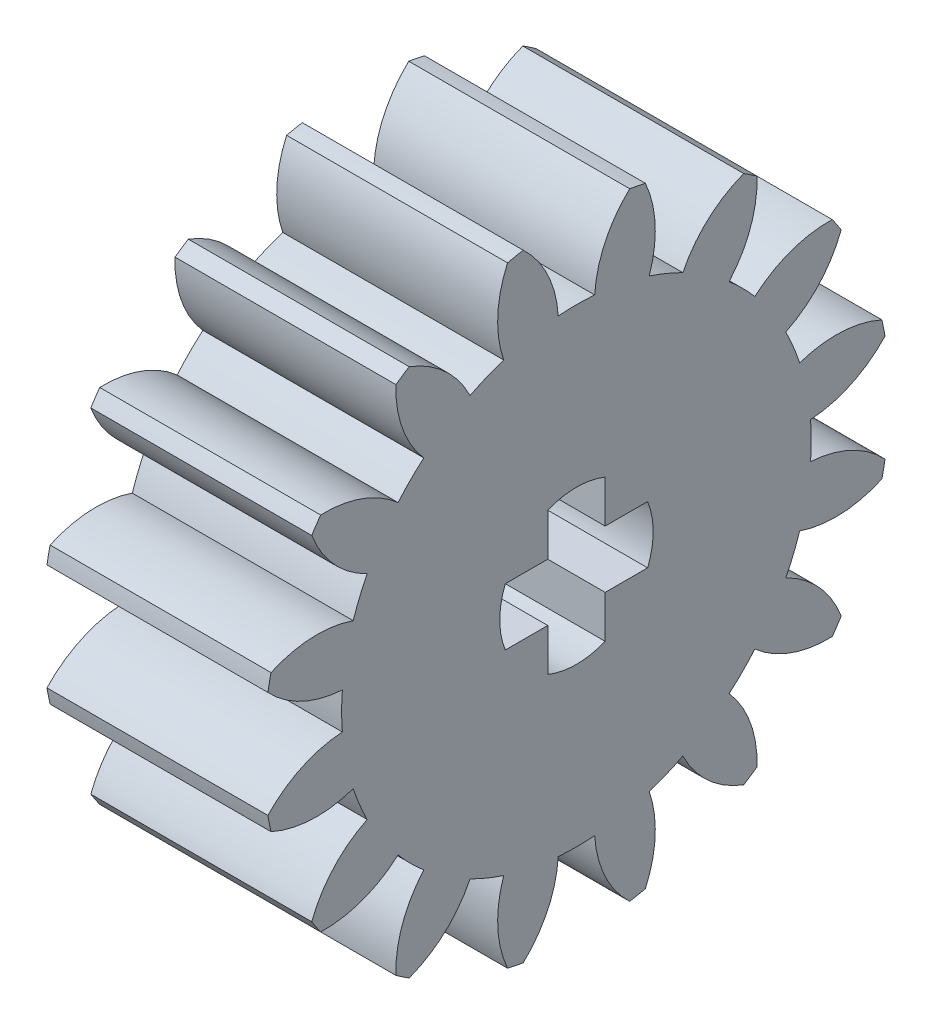
SolidWorks part; units mm, degrees
ref_plane "Plane1" through (0, 0, 0) normal (0, 0, 1) x (1, 0, 0)
ref_plane "Plane2" through (0, 0, 0) normal (0, 1, 0) x (1, 0, 0)
ref_plane "Plane3" through (0, 0, 0) normal (1, 0, 0) x (0, 0, -1)
sketch "HoldingSke" plane through (0, 0, 0) normal (0, 1, 0) x (1, 0, 0)
  line L0 (0, 0) -> (0.9613, -0.2756)
  line L1 (-15, 0) -> (100, 0) construction
  line L2 (0, 0) -> (-2.1039, 2.3779)
  line L3 (0, 0) -> (-11.863, 4.5341)
  line L4 (0, 0) -> (8.3015, 2.3804)
  line L5 (0, 0) -> (-46.8476, -17.4728)
  line L6 (0, 0) -> (-5.2639, -3.5516)
  line L7 (-2.1039, 2.3779) -> (8.6588, 51.2067)
  line L8 (-76.2, 54.61) -> (-76.1, 54.61)
  line L9 (-71.009, 38.7566) -> (-53.1078, 45.2721)
  line L10 (-76.2, 71.12) -> (104.1128, 71.12)
  line L11 (0, 0) -> (-6.35, 0)
  line L12 (-76.2, 101.6) -> (-76.162, 101.6)
  line L13 (24.9733, 27.94) -> (52.9518, 28.4284)
  line L14 (24.9733, 27.94) -> (24.9743, 27.94)
  line L15 (24.9733, 27.94) -> (100.4006, 29.5858)
  line L16 (-63.627, -1) -> (-12.827, -1)
  circle A0 centre (0, 0) radius 0.5
  circle A1 centre (0, 0) radius 6.749
  circle A2 centre (0, 0) radius 37.5
  circle A3 centre (0, 0) radius 0.5
  dimension "MHD" = 13.498
  dimension "Hub_dia" = 75
  dimension "Bore" = 1
  dimension "MBD" = 1
  dimension "Num_teeth" = 16
  dimension "Pitch_radius" = 180.3128
  dimension "Pitch" = 1
  dimension "Width" = 6.35
  dimension "Overall_len" = 50
  dimension "Show_teeth" = 16
  dimension "Thickness" = 6.35
  dimension "OAL" = 50.0009
  dimension "T_dim" = 0.1
  dimension "Ap" = 20
  dimension "H" = 19.05
  dimension "Backlash" = 0.038
  dimension "Addendum_fac" = 1
  dimension "Dedendum_fac" = 1.25
  dimension "Clearance_fac" = 0.25
  dimension "Dedendum_add" = 0.001
  dimension "Module" = 1
sketch "BasProSke" plane through (0, 0, 0) normal (0, 1, 0) x (1, 0, 0)
  line L0 (-10, 0) -> (60, 0) construction
  line L1 (0, 0) -> (0, 9)
  line L2 (0, 0) -> (6.35, 0)
  line L3 (6.35, 0) -> (6.35, 9)
  line L4 (6.35, 9) -> (0, 9)
  dimension "Diameter" = 18
  dimension "Thickness" = 6.35
revolve "Base-Revolve" add sketch "BasProSke" angle 360 about L0
sketch "TooCutSke" plane through (0, 0, 0) normal (1, 0, 0) x (0, 0, -1)
  line L1 (0, 0) -> (0, 107) construction
  line L2 (0, 0) -> (-0.8506, 7.9547) construction
  line L3 (0, 0) -> (-3.1089, 15.6293) construction
  line L4 (-0.8506, 7.9547) -> (-1.5544, 7.8146) construction
  arc A0 (0.5238, 6.7286) -> (-0.5238, 6.7286) centre (0, 0) ccw
  arc A1 (1.5534, 8.8907) -> (-1.5534, 8.8907) centre (0, 0) ccw
  circle A2 centre (0, 0) radius 8 construction
  circle A3 centre (0, 0) radius 7.5175 construction
  arc A4 (-0.5238, 6.7286) -> (-1.5534, 8.8907) centre (-3.7179, 6.5338) ccw
  arc A5 (1.5534, 8.8907) -> (0.5238, 6.7286) centre (3.7179, 6.5338) ccw
  dimension "Root_dia" = 13.498
  dimension "Overcut_dia" = 18.0508
  dimension "Pitch_dia" = 16
  dimension "Base_dia" = 15.0351
  dimension "Flank_rad" = 3.2
  dimension "Half_ang" = 11.25
  dimension "Half_CT" = 0.7176
extrude "ToothCut" cut sketch "TooCutSke" along normal through all
fillet "Breaks" [suppressed] radius 0.02
fillet "RootFillets" [suppressed] radius 0.251
pattern_circular "TeethCuts" count 16 every 22.5 about axis through (-10, 0, 0) along (1, 0, 0) of "ToothCut", "RootFillets", "Breaks"
sketch "HubNeaOneSke" plane through (0, 0, 0) normal (-1, 0, 0) x (0, 0, 1)
  circle A0 centre (0, 0) radius 6.749
  dimension "Diameter" = 13.498
extrude "HubNearOne" [suppressed] add sketch "HubNeaOneSke" along normal blind 43.6509
sketch "HubNeaBotSke" plane through (0, 0, 0) normal (-1, 0, 0) x (0, 0, 1)
  circle A0 centre (0, 0) radius 6.749
  dimension "Diameter" = 13.498
extrude "HubNearBoth" [suppressed] add sketch "HubNeaBotSke" along normal blind 21.8254
ref_plane "FarPln" through (6.35, 0, 0) normal (1, 0, 0) x (0, 0, -1)
sketch "HubFarSke" plane through (6.35, 0, 0) normal (1, 0, 0) x (0, 0, -1)
  circle A0 centre (0, 0) radius 6.749
  dimension "Diameter" = 13.498
extrude "HubFar" [suppressed] add sketch "HubFarSke" along normal blind 21.8254
sketch "BorSke" plane through (0, 0, 0) normal (1, 0, 0) x (0, 0, -1)
  circle A0 centre (0, 0) radius 0.5
  dimension "Diameter" = 1
extrude "Bore" cut sketch "BorSke" along normal mid plane 100.0017
sketch "KeySke" plane through (0, 0, 0) normal (1, 0, 0) x (0, 0, -1)
  line L0 (-0.05, 0) -> (-0.05, 0.6)
  line L1 (-0.05, 0.6) -> (0.05, 0.6)
  line L2 (0.05, 0.6) -> (0.05, 0)
  line L3 (0, 0) -> (0, 34) construction
  line L4 (-0.05, 0) -> (0.05, 0)
  dimension "Offset" = 0.6
  dimension "Width" = 0.1
extrude "Keyway" [suppressed] cut sketch "KeySke" along normal mid plane 100.0017
pattern_circular "Keyway2" [suppressed] count 2 every 90 about axis through (-10, 0, 0) along (1, 0, 0)
sketch "Sketch1" plane through (6.35, 0, 0) normal (1, 0, 0) x (0, 0, -1)
  line L0 (-0.8249, 2.0449) -> (-0.8249, 0.8249)
  line L1 (-0.8249, 0.8249) -> (-2.0449, 0.8249)
  line L2 (-2.0449, -0.8249) -> (-0.8249, -0.8249)
  line L3 (-0.8249, -0.8249) -> (-0.8249, -2.0449)
  line L4 (0.8249, -2.0449) -> (0.8249, -0.8249)
  line L5 (0.8249, -0.8249) -> (2.0449, -0.8249)
  line L6 (2.0449, 0.8249) -> (0.8249, 0.8249)
  line L7 (0.8249, 0.8249) -> (0.8249, 2.0449)
  circle A0 centre (0, 0) radius 2.205
  dimension "D1" = 4.41
  dimension "D2" = 1.22
extrude "Cut-Extrude1" cut sketch "Sketch1" against normal blind 10 contours L7 A0 L0 L1 L2 L3 L4 L5 L6
equation "' \"Module@HoldingSke\" = 6.35"
equation "' \"Num_teeth@HoldingSke\" = 12"
equation "' \"Ap@HoldingSke\" =  20"
equation "' \"Width@HoldingSke\" = 0.5 * 25.4"
equation "' \"Hub_dia@HoldingSke\"= 1 * 25.4"
equation "' \"Overall_len@HoldingSke\" = 1.0 * 25.4"
equation "' \"Bore@HoldingSke\" = 0.75 * 25.4"
equation "' \"T_dim@HoldingSke\" = 0.1 * 25.4"
equation "' \"Width@KeySke\" = 0.25 * 25.4"
equation "' \"Show_teeth@HoldingSke\" = 13"
equation "' \"Backlash@HoldingSke\" = 0.009 * 25.4"
equation "' \"Addendum_fac@HoldingSke\" = 1.0"
equation "' \"Dedendum_fac@HoldingSke\" = 1.25"
equation "' \"Dedendum_add@HoldingSke\" = 0.00005 * 25.4"
equation "' \"Clearance_fac@HoldingSke\" = 0.25"
equation "\"Pitch@HoldingSke\" = 1 / \"Module@HoldingSke\""
equation "\"Overcut_dia@TooCutSke\" = (\"Num_teeth@HoldingSke\" + 2 * \"Addendum_fac@HoldingSke\") / \"Pitch@HoldingSke\" + 0.002 * 25.4"
equation "\"Pitch_dia@TooCutSke\" = \"Num_teeth@HoldingSke\" / \"Pitch@HoldingSke\""
equation "\"Base_dia@TooCutSke\" = \"Num_teeth@HoldingSke\" / \"Pitch@HoldingSke\" * cos((\"Ap@HoldingSke\"  * 3.14159265 / 180))"
equation "\"Root_dia@TooCutSke\" = (\"Num_teeth@HoldingSke\" + 2) / \"Pitch@HoldingSke\" - 2 * (\"Addendum_fac@HoldingSke\" + \"Dedendum_fac@HoldingSke\") / \"Pitch@HoldingSke\" - \"Dedendum_add@HoldingSke\" * 2"
equation "\"Half_ang@TooCutSke\" = 180 / \"Num_teeth@HoldingSke\""
equation "\"Half_CT@TooCutSke\" = \"Num_teeth@HoldingSke\" / \"Pitch@HoldingSke\" * sin((3.14159265 / 2 / \"Num_teeth@HoldingSke\")) / 2 - 7 * \"Backlash@HoldingSke\" / 4"
equation "\"Flank_rad@TooCutSke\" = \"Num_teeth@HoldingSke\" / \"Pitch@HoldingSke\" / 5"
equation "\"Radius@RootFillets\" = \"Clearance_fac@HoldingSke\" / \"Pitch@HoldingSke\" + \"Dedendum_add@HoldingSke\""
equation "\"Break_rad@Breaks\" = 0.02 / \"Pitch@HoldingSke\""
equation "\"Thickness@HoldingSke\" = \"Width@HoldingSke\""
equation "\"OAL@HoldingSke\" = \"Thickness@HoldingSke\""
equation "\"MHD@HoldingSke\" = (\"Num_teeth@HoldingSke\" + 2) / \"Pitch@HoldingSke\" - 2 * (\"Addendum_fac@HoldingSke\" + \"Dedendum_fac@HoldingSke\")  / \"Pitch@HoldingSke\" - \"Dedendum_add@HoldingSke\" * 2"
equation "\"MBD@HoldingSke\" = (\"Num_teeth@HoldingSke\" + 2) / \"Pitch@HoldingSke\" - 2 * (\"Addendum_fac@HoldingSke\" + \"Dedendum_fac@HoldingSke\")  / \"Pitch@HoldingSke\" - \"Dedendum_add@HoldingSke\" * 2 - 0.002 * 25.4"
equation "\"MHD@HoldingSke\" = ((sgn( \"MHD@HoldingSke\" - \"Hub_dia@HoldingSke\" )-1)*( \"MHD@HoldingSke\" - \"Hub_dia@HoldingSke\" ))/-2+ \"Hub_dia@HoldingSke\""
equation "\"MBD@HoldingSke\" = ((sgn( \"MBD@HoldingSke\" - \"Bore@HoldingSke\" )-1)*( \"MBD@HoldingSke\" - \"Bore@HoldingSke\" ))/-2+ \"Bore@HoldingSke\""
equation "\"OAL@HoldingSke\" = ((sgn( \"OAL@HoldingSke\" - \"Overall_len@HoldingSke\" )+1)*( \"OAL@HoldingSke\" - \"Overall_len@HoldingSke\" ))/2 + \"Overall_len@HoldingSke\" + 0.000002 * 25.4"
equation "\"Num_teeth@TeethCuts\" = int( \"Show_teeth@HoldingSke\" ) + 1"
equation "\"Num_teeth@TeethCuts\" = ((sgn( \"Num_teeth@TeethCuts\" - \"Num_teeth@HoldingSke\" )-1)*( \"Num_teeth@TeethCuts\" - \"Num_teeth@HoldingSke\" ))/-2+ \"Num_teeth@HoldingSke\""
equation "\"Num_teeth@TeethCuts\" = ((sgn( \"Num_teeth@TeethCuts\" - 2.0)+1)*( \"Num_teeth@TeethCuts\" - 2.0))/2 +2.0"
equation "\"Angle@TeethCuts\" = 360.0 / \"Num_teeth@HoldingSke\""
equation "\"Diameter@BasProSke\" = (\"Num_teeth@HoldingSke\" + 2 * \"Addendum_fac@HoldingSke\") / \"Pitch@HoldingSke\""
equation "\"Thickness@BasProSke\"  = \"Thickness@HoldingSke\""
equation "' \"Fillet_rad@BasProSke\" =  \"Thickness@HoldingSke\" * 0.05"
equation "\"MHD@HoldingSke\" = ((sgn( \"MHD@HoldingSke\" - \"Root_dia@TooCutSke\" )-1)*( \"MHD@HoldingSke\" - \"Root_dia@TooCutSke\" ))/-2+ \"Root_dia@TooCutSke\""
equation "\"Diameter@HubNeaOneSke\" = \"MHD@HoldingSke\""
equation "\"Length@HubNearOne\" = \"OAL@HoldingSke\" - \"Thickness@BasProSke\""
equation "\"Diameter@HubNeaBotSke\" = \"MHD@HoldingSke\""
equation "\"Length@HubNearBoth\" = ( \"OAL@HoldingSke\" - \"Thickness@BasProSke\" ) / 2.0"
equation "\"Thickness@FarPln\" = \"Thickness@BasProSke\""
equation "\"Diameter@HubFarSke\" = \"MHD@HoldingSke\""
equation "\"Length@HubFar\" = ( \"OAL@HoldingSke\" - \"Thickness@BasProSke\" ) / 2.0"
equation "\"Diameter@BorSke\" = \"MBD@HoldingSke\""
equation "\"D1@Bore\" = \"OAL@HoldingSke\" * 2.0"
equation "\"D1@Keyway\" = \"OAL@HoldingSke\" * 2.0"
equation "\"Offset@KeySke\" = \"T_dim@HoldingSke\" + \"MBD@HoldingSke\" / 2.0"
equation "\"CageLeftBottomEdge\"=22.11mm"
equation "\"CageLeftTopEdge\"=22.11mm"
equation "\"CageRightBottomEdge\"=21.63mm"
equation "\"CageRightTopEdge\"=21.63mm"
equation "\"CageHeight\"=86.04mm"
equation "\"CageLength\"=73.76mm"
equation "\"CageTopScrewClearance\"=10mm"
equation "\"CageBottomScrewClearance\"=25mm"
equation "\"CageLeftTopDepth\"= 11.65mm"
equation "\"CageLeftBottomDepth\"=11.11mm"
equation "\"CageLeftTopHeight\"=8.56175mm"
equation "\"CageLeftBottomHeight\"=16mm"
equation "\"CageRightTopDepth\"= 11.05mm"
equation "\"CageRightBottomDepth\"=10.58mm"
equation "\"CageRightTopHeight\"=9.6mm"
equation "\"CageRightBottomHeight\"=15.49mm"
equation "\"CageLeftTopChannelDepth\"=2.41908mm"
equation "\"CageLeftBottomChannelDepth\"=2.588mm"
equation "\"CageLeftChannelHeight\"=11.7mm"
equation "\"CageRightTopChannelDepth\"=2.32mm"
equation "\"CageRightBottomChannelDepth\"=2.318mm"
equation "\"CageRightChannelHeight\"=10mm"
equation "\"CageChanRelHeight\"=23.99mm"
equation "\"CageChanRelDepth\"=5.492mm"
equation "\"CageChamberRadius\"=16.261mm"
equation "\"CageScrewDiameter\"=4.8mm"
equation "\"CageSetScrewDiameter\"=3.5mm"
equation "\"CageAxleRadius\"=6.639mm"
equation "\"CageAxleKeyHeight\"=1.619mm"
equation "\"CageAxleKeyWidth\"=2.662mm"
equation "\"CageHoseWindowWidth\"=16.29mm"
equation "\"CageHoseWindowHeight\"=26.5mm"
equation "\"CageHoseWindow-Edge\"=8.89mm"
equation "\"CageScrew-VerticalEdge\"=5.0mm"
equation "\"CageScrew-HorizontalEdge\"=7.5mm"
equation "\"CageScrew-HoseCornerScrewEdge\"=4.45mm"
equation "\"CageAxle-BottomEdge\"=56.05mm"
equation "\"CageAxle-FrontEdge\"=46.03mm"
equation "\"CageBackSetScrew-Axle\"=40mm"
equation "\"CageFrontSetScrew-Axle\"=22mm"
equation "\"CageVelocityWindow-BackEdge\"=34.8mm"
equation "\"CageVelocityWindow-BottomEdge\"=27.55mm"
equation "\"CageVelocityWindowHeight\"=22.29mm"
equation "\"CageVelocityWindowWidth\"=12.61mm"
equation "\"TriggerSlot-BottomEdge\"=6.35mm"
equation "\"TriggerSlot-FrontEdge\"=15mm"
equation "\"TriggerSlotSize\"=6.7mm"
equation "\"TriggerRackOffset\"=6mm"
equation "\"TriggerSlotSizeInt\"=.25in"
equation "\"MotorMountLegLength\"=.25in"
equation "\"GearOffset\"=.264907in"
equation "\"TriggerSlotSpacing\"=.25in"
equation "\"TriggerMiniSlotWidth\"=3.5mm"
equation "\"TriggerRackWidth\"=6.5mm"
equation "\"gearhubintdiam\"=30mm"
equation "\"gearhubintwid\"=15mm"
equation "\"vigorwidth\"= 0.472441in"
equation "\"vigorflangewidth\"= 0.731102in"
equation "\"vigorflangelength\"= 0.131102in"
equation "\"vigorscrewsize\"= 0.066535in"
equation "\"vigorholeoffsetwid\"= 0.0646653in"
equation "\"vigorholeoffsetlen\"= 0.065551in"
equation "\"vigorflangedepth\"= 0.0901575in"
equation "\"vigordiscdepth\"= 0.0492126in"
equation "\"vigormotordepth\"= 1.12362in"
equation "\"vigortipdepth\"= 0.259055in"
equation "\"vigoraxlewidth\"= 0.173622in"
equation "\"vigorcutlen\"= 0.0480315in"
equation "\"vigoraxledepth\"= 0.159055in"
equation "\"pandiscradius\"=14in"
equation "\"towermaterialwidth\"=.25in"
equation "\"towerslotlength\"=.5in"
equation "\"towermarkerspace\"=5in"
equation "\"towerslothorizoffset\"=1in"
equation "\"towerslothorizspacing\"=2in"
equation "\"towerslotvertoffset\"=3in"
equation "\"towerslotvertspacing\"=1in"
equation "\"towerheight\"=12in"
equation "\"towerupslot\"=1in"
equation "\"toweraxle\"=.5in"
equation "\"towerspeedwidth\"=2in"
equation "\"towerspeedheight\"=8in"
equation "\"towerspeedgap\"=2in"
equation "\"stepperouterrad\"=10mm"
equation "\"stepperscrewsize\"=3.45mm"
equation "\"stepperscrewc2c\"=49.5mm"
equation "\"stepperdepthoffset\"=24mm"
equation "\"stepperhorizoffset\"=22.91mm"
equation "\"stepperaxleflat\"=.037in"
equation "\"stepperaxlerad\"=0.11811024in"
equation "\"shaftslotOD\"=18.8mm"
equation "\"shaftslotID\"=13.28mm"
equation "\"shaftkeywidth\"=2.67mm"
equation "\"shaftkeydepth\"=1.8mm"
equation "\"shaftcollartotaldepth\"=12.5mm"
equation "\"shaftsquaredepth\"=6mm"
equation "\"shaftsetscrewsize\"=3.5mm"
equation "\"shaftkeytightdepth\"=1.85mm"
equation "\"shaftslottightID\"=12.78mm"
equation "\"shaftsetscrewoffset\"=9mm"
equation "\"cagecollartotaldepth\"=10mm"
equation "\"cagecollartotalwidth\"=35mm"
equation "\"cagecollarbasedepth\"=4mm"
equation "\"ajaxaxlesize\"=3.87mm"
equation "\"ajaxinnercut\"=2.3mm"
equation "\"ajaxwidth\"=6.1mm"
equation "\"ajaxdiametral\"=25.8854"
equation "\"ajaxcutoutdepth\"=2.3mm"
equation "\"ajax4020gap\"=29.5mm"
equation "\"ajax4010gap\"=24.5mm"
equation "\"ajax20hubbuffer\"=6.1mm"
equation "\"ajax20hubholeoffset\"=.19685in"
equation "\"ajax20hubholesize\"=.059055in"
equation "\"ajax20cutoutint\"=13.4mm"
equation "\"ajax40hubholesize\"=7.21mm"
equation "\"ajax40hubholeoffset\"=10mm"
equation "\"ajax40hubbuffer\"=8.9mm"
equation "\"ajax40cutoutint\"=32.6mm"
equation "\"bearingpandiscrad\"=6.8in"
equation "\"bearingpandiscang\"=48.75deg"
equation "\"bearingclearholedist\"=4.7345in"
equation "\"bearingclearholesize\"=.5in"
equation "\"bearingclearholeang\"=22.5deg"
equation "\"bearingmountholedist\"=4.25in"
equation "\"bearingwirehole\"=1.5in"
equation "\"no6diam\"=.146in"
equation "\"shortconangle\"=20deg"
equation "\"shortconlen\"=.875in"
equation "\"longconlen\"=1.25in"
equation "\"longconangle\"=15deg"
equation "\"D1@Sketch1\"=\"vigoraxlewidth\""
equation "\"D2@Sketch1\"=\"vigorcutlen\""
